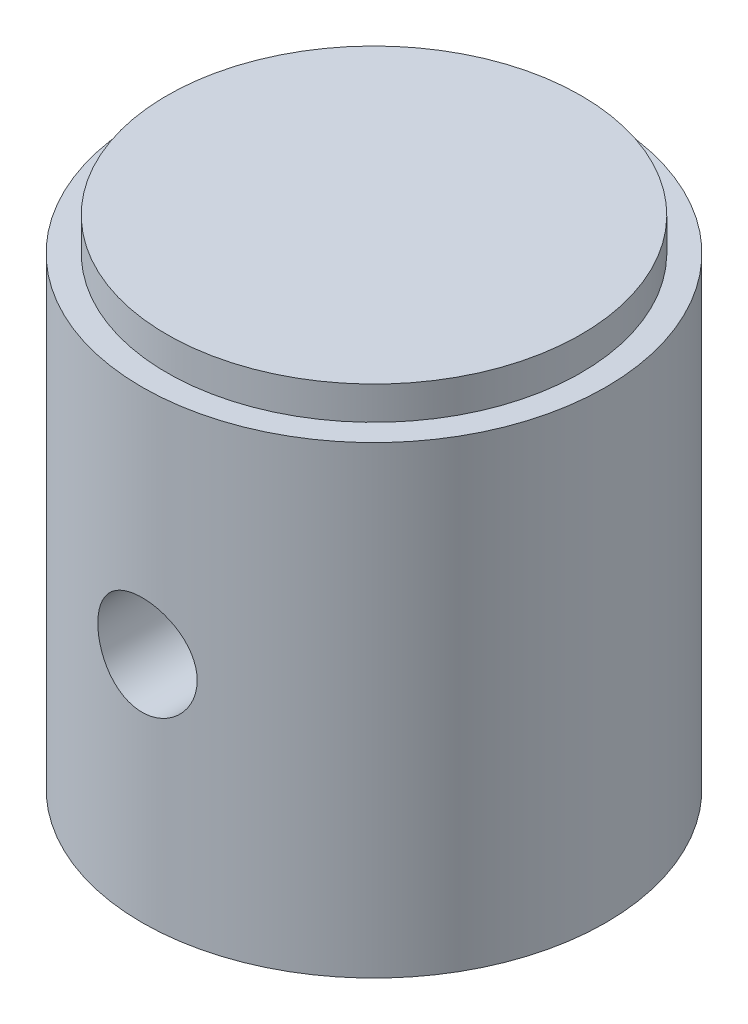
SolidWorks part; units mm, degrees
ref_plane "Front Plane" through (0, 0, 0) normal (0, 0, 1) x (1, 0, 0)
ref_plane "Top Plane" through (0, 0, 0) normal (0, 1, 0) x (1, 0, 0)
ref_plane "Right Plane" through (0, 0, 0) normal (1, 0, 0) x (0, 0, -1)
sketch "Эскиз1" plane through (0, 0, 0) normal (0, 0, 1) x (1, 0, 0)
  line L0 (0, 0) -> (0, 15) construction
  line L1 (-4.75, 3.9838) -> (-4.75, 11)
  line L2 (-7, 0) -> (-7, 14)
  line L3 (-7, 14) -> (-6.25, 14)
  line L4 (-6.25, 15) -> (-6.25, 14)
  line L5 (-6.25, 15) -> (0, 15)
  line L6 (-7, 0) -> (-6.2, 0)
  line L7 (-6.2, 0) -> (-4.75, 3.9838)
  line L8 (-4.75, 11) -> (0, 13.8541)
  line L9 (0, 15) -> (0, 13.8541)
  dimension "D1" = 7
  dimension "D2" = 6.25
  dimension "D3" = 4.75
  dimension "D4" = 6.2
  dimension "D5" = 20
  dimension "D6" = 1
  dimension "D7" = 11
  dimension "D8" = 59
  dimension "D9" = 15
revolve "Повернуть1" add sketch "Эскиз1" angle 360 about L0
sketch "Эскиз2" plane through (0, 0, 0) normal (0, 0, 1) x (1, 0, 0)
  line L0 (0, 0) -> (0, 9.4804) construction
  circle A0 centre (0, 7) radius 1.5
  dimension "D1" = 3
  dimension "D2" = 7
extrude "Вырез-Вытянуть1" cut sketch "Эскиз2" against normal through all both and the other way through all
